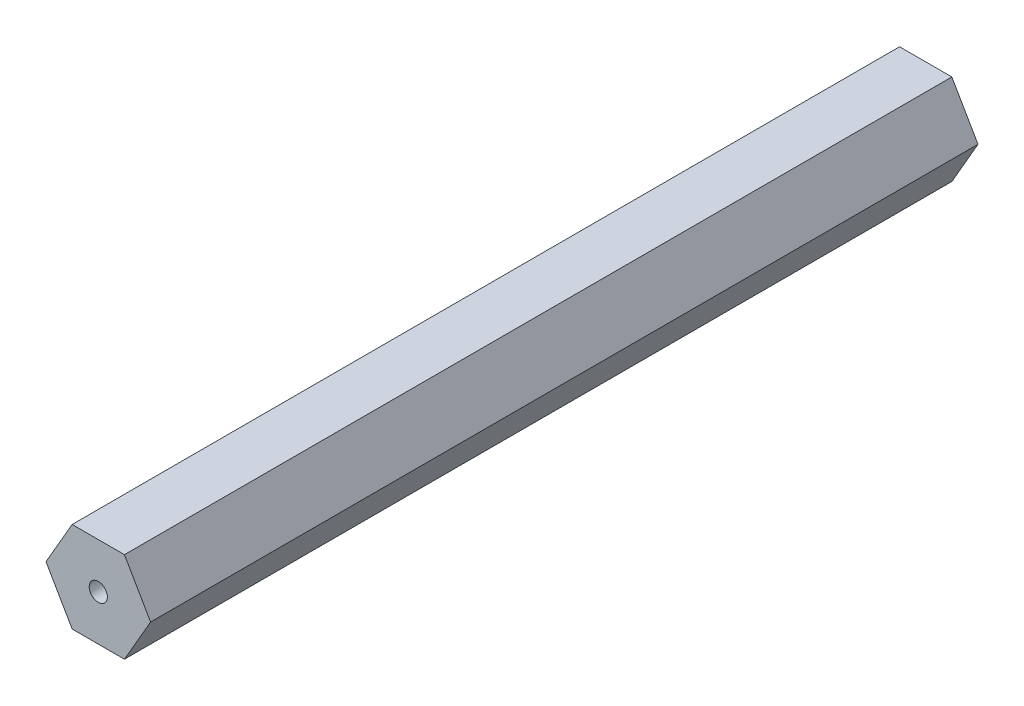
SolidWorks part; units mm, degrees
ref_plane "Front Plane" through (0, 0, 0) normal (0, 0, 1) x (1, 0, 0)
ref_plane "Top Plane" through (0, 0, 0) normal (0, 1, 0) x (1, 0, 0)
ref_plane "Right Plane" through (0, 0, 0) normal (1, 0, 0) x (0, 0, -1)
sketch "Sketch1" plane through (0, 0, 0) normal (0, 0, 1) x (1, 0, 0)
  line L1 (7.3323, 0) -> (3.6662, 6.35)
  line L2 (3.6662, 6.35) -> (-3.6662, 6.35)
  line L3 (-3.6662, 6.35) -> (-7.3323, 0)
  line L4 (-7.3323, 0) -> (-3.6662, -6.35)
  line L5 (-3.6662, -6.35) -> (3.6662, -6.35)
  line L6 (3.6662, -6.35) -> (7.3323, 0)
  circle A0 centre (0, 0) radius 1.27
  circle A1 centre (0, 0) radius 6.35 construction
  dimension "D1" = 12.7
  dimension "D2" = 2.54
extrude "Boss-Extrude1" add sketch "Sketch1" along normal blind 116.0272
